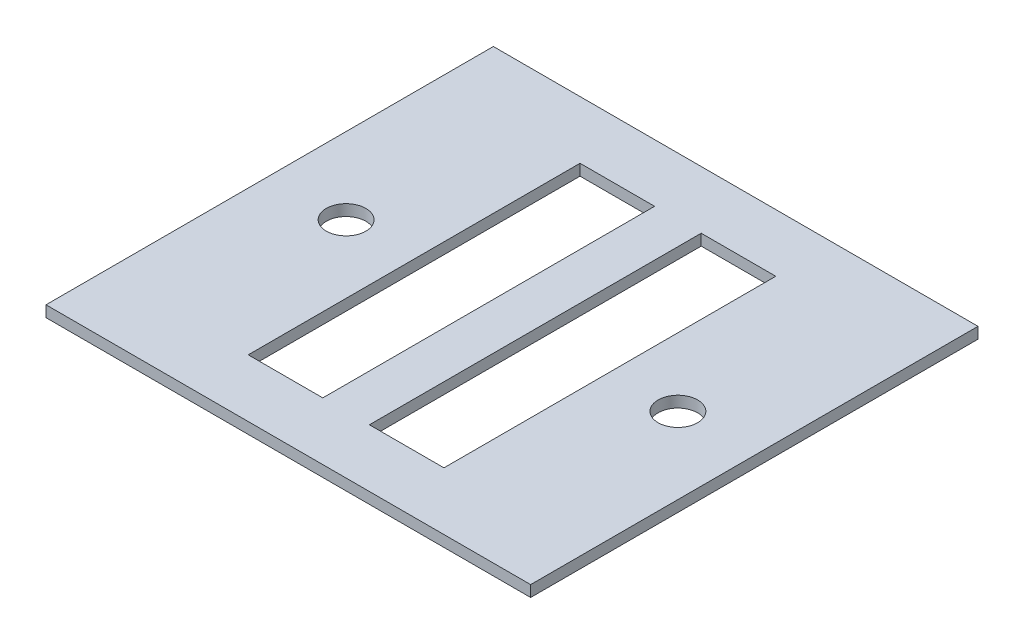
SolidWorks part; units mm, degrees
ref_plane "Front Plane" through (0, 0, 0) normal (0, 0, 1) x (1, 0, 0)
ref_plane "Top Plane" through (0, 0, 0) normal (0, 1, 0) x (1, 0, 0)
ref_plane "Right Plane" through (0, 0, 0) normal (1, 0, 0) x (0, 0, -1)
sketch "Sketch1" plane through (0, 0, 0) normal (0, 1, 0) x (1, 0, 0)
  line L1 (-65, -60) -> (65, -60)
  line L2 (-65, -60) -> (-65, 60)
  line L3 (-65, 60) -> (65, 60)
  line L4 (65, -60) -> (65, 60)
  line L5 (-65, -60) -> (65, 60) construction
  line L6 (-65, 60) -> (65, -60) construction
  point P0 (0, 0)
  dimension "D1" = 130
  dimension "D2" = 120
extrude "Boss-Extrude1" add sketch "Sketch1" along normal blind 3
sketch "Sketch2" plane through (0, 3, 0) normal (0, 1, 0) x (1, 0, 0)
  line L1 (-26.25, -44.5) -> (-6.25, -44.5)
  line L2 (-26.25, -44.5) -> (-26.25, 44.5)
  line L3 (-26.25, 44.5) -> (-6.25, 44.5)
  line L4 (-6.25, -44.5) -> (-6.25, 44.5)
  line L5 (-26.25, -44.5) -> (-6.25, 44.5) construction
  line L6 (-26.25, 44.5) -> (-6.25, -44.5) construction
  point P0 (-16.25, 0)
  dimension "D1" = 89
  dimension "D2" = 20
  dimension "D3" = 6.25
extrude "Cut-Extrude1" cut sketch "Sketch2" against normal through all both and the other way through all
mirror "Mirror1" about plane through (0, 0, 0) normal (1, 0, 0) of "Cut-Extrude1"
sketch "Sketch3" plane through (0, 3, 0) normal (0, 1, 0) x (1, 0, 0)
  circle A0 centre (44.5, 0) radius 5.3
  dimension "D1" = 10.6
  dimension "D2" = 44.5
extrude "Cut-Extrude2" cut sketch "Sketch3" against normal through all both and the other way through all
mirror "Mirror2" about plane through (0, 0, 0) normal (1, 0, 0) of "Cut-Extrude2"
